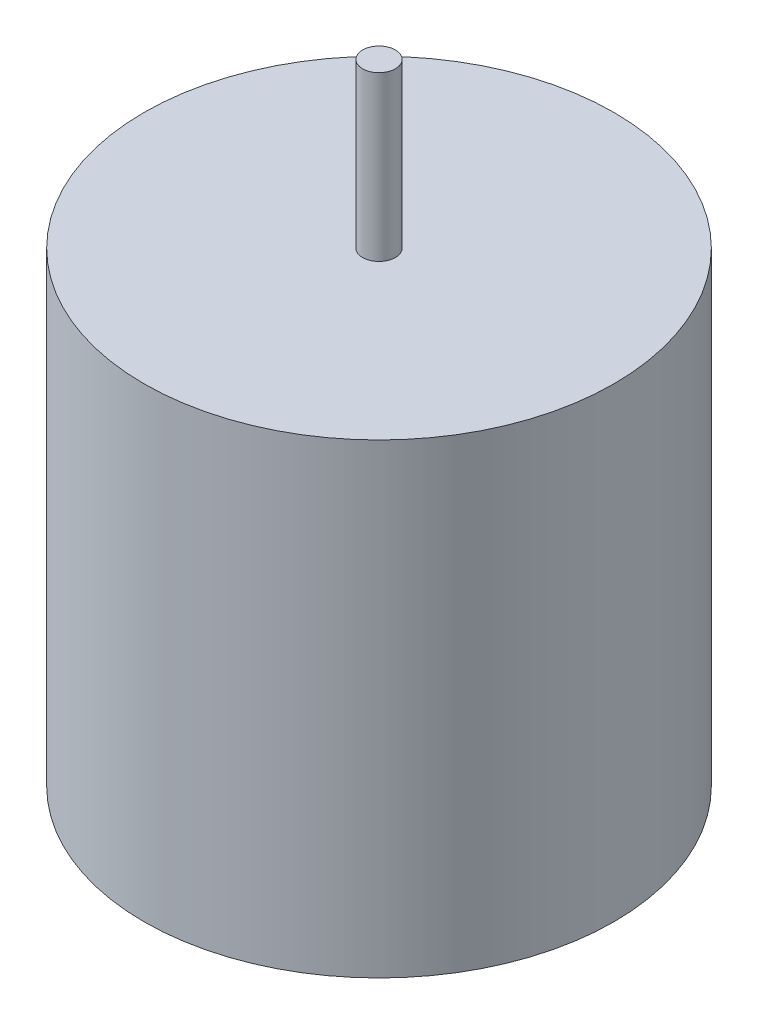
SolidWorks part; units mm, degrees
ref_plane "Plan de face" through (0, 0, 0) normal (0, 0, 1) x (1, 0, 0)
ref_plane "Plan de dessus" through (0, 0, 0) normal (0, 1, 0) x (1, 0, 0)
ref_plane "Plan de droite" through (0, 0, 0) normal (1, 0, 0) x (0, 0, -1)
sketch "Esquisse1" plane through (0, 0, 0) normal (0, 1, 0) x (1, 0, 0)
  circle A0 centre (0, 0) radius 4
  circle A1 centre (0, 0) radius 34.9165 construction
  dimension "D1" = 8
extrude "Boss.-Extru.1" add sketch "Esquisse1" along normal blind 40
sketch "Esquisse2" plane through (0, 0, 0) normal (0, -1, 0) x (1, 0, 0)
  circle A0 centre (0, 0) radius 57.5
  dimension "D1" = 115
extrude "Boss.-Extru.2" add sketch "Esquisse2" along normal blind 114
